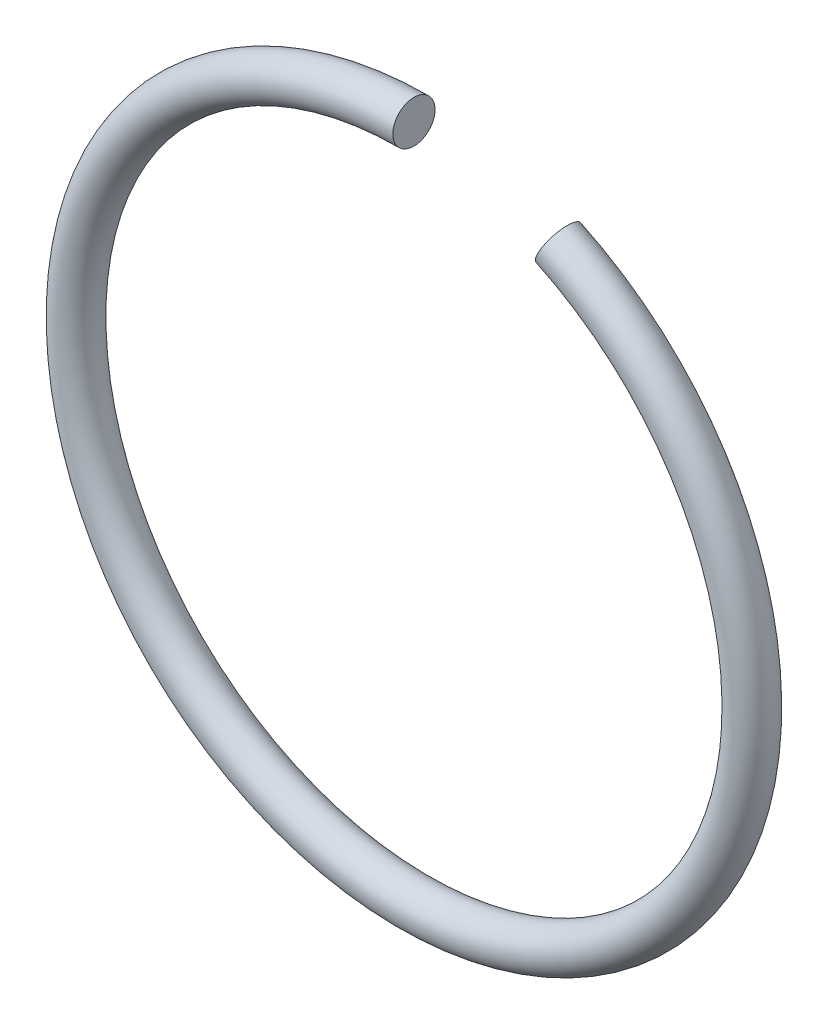
SolidWorks part; units mm, degrees
material "1.0601 (C60)"
ref_plane "Front Plane" through (0, 0, 0) normal (0, 0, 1) x (1, 0, 0)
ref_plane "Top Plane" through (0, 0, 0) normal (0, 1, 0) x (1, 0, 0)
ref_plane "Right Plane" through (0, 0, 0) normal (1, 0, 0) x (0, 0, -1)
sketch "Sketch1" plane through (0, 0, 0) normal (0, 0, 1) x (1, 0, 0)
  line L0 (0, 8) -> (0, 0) construction
  line L1 (3.4152, 7.2344) -> (0, 0) construction
  arc A0 (0, 8) -> (3.4152, 7.2344) centre (0, 0) ccw
  dimension "D1" = 3.5
  dimension "D2" = 8
sketch "Sketch2" plane through (0, 0, 0) normal (1, 0, 0) x (0, 0, -1)
  line L0 (0, 8) -> (0, -8) construction
  line L1 (0, 8) -> (0, -8) construction
  circle A0 centre (0, 8) radius 0.5
  dimension "D1" = 1
  dimension "D2" = 16
sweep "Sweep1" add profiles "Sketch2" path "Sketch1"
